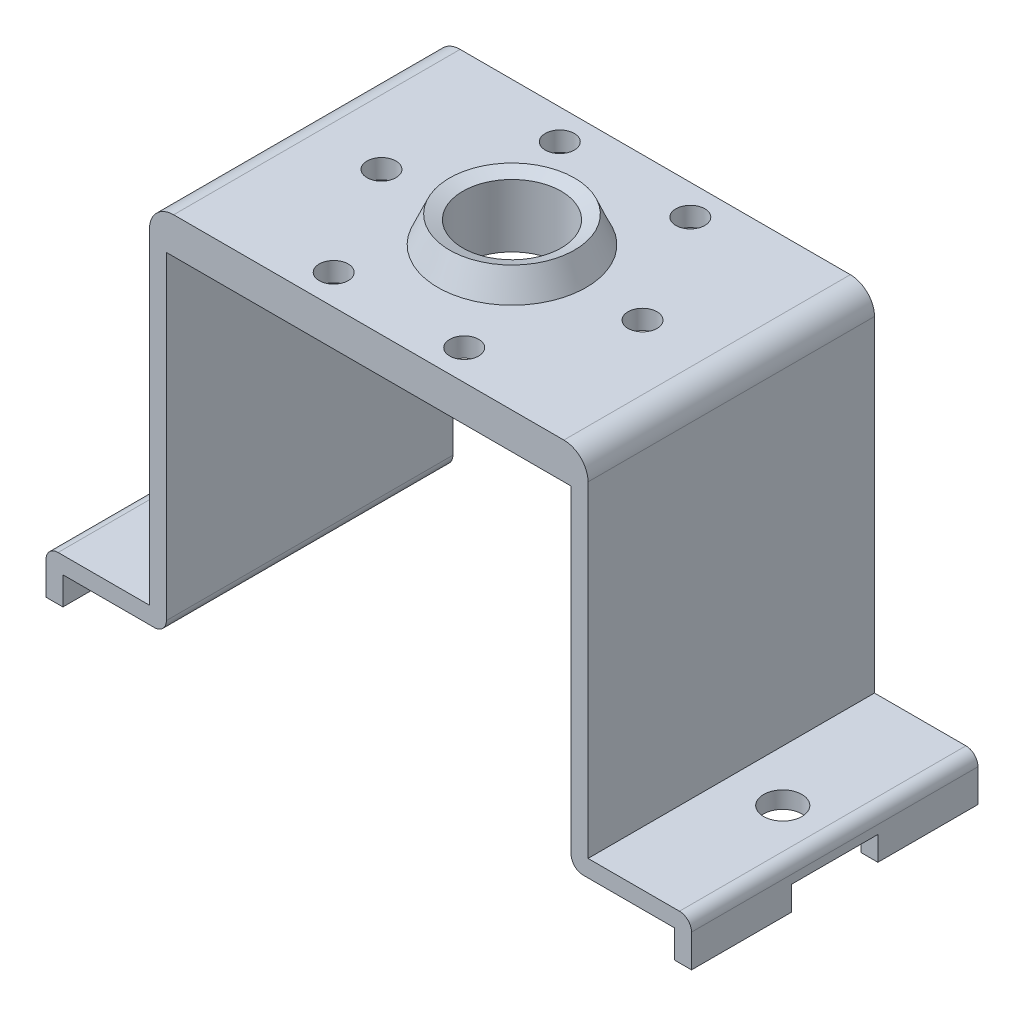
SolidWorks part; units mm, degrees
ref_plane "Front Plane" through (0, 0, 0) normal (0, 0, 1) x (1, 0, 0)
ref_plane "Top Plane" through (0, 0, 0) normal (0, 1, 0) x (1, 0, 0)
ref_plane "Right Plane" through (0, 0, 0) normal (1, 0, 0) x (0, 0, -1)
sketch "Sketch1" plane through (0, 0, 0) normal (0, 1, 0) x (1, 0, 0)
  line L1 (-17.9768, -15.0622) -> (17.9768, -15.0622)
  line L2 (-23.0568, -9.9822) -> (-23.0568, 9.9822)
  line L3 (-17.9768, 15.0622) -> (17.9768, 15.0622)
  line L4 (23.0569, -9.9822) -> (23.0569, 9.9822)
  line L5 (-23.0568, -15.0622) -> (23.0569, 15.0622) construction
  line L6 (-23.0568, 15.0622) -> (23.0569, -15.0622) construction
  arc A0 (-17.9768, -15.0622) -> (-23.0568, -9.9822) centre (-17.9768, -9.9822) cw
  arc A1 (17.9768, -15.0622) -> (23.0569, -9.9822) centre (17.9769, -9.9822) ccw
  arc A2 (17.9768, 15.0622) -> (23.0569, 9.9822) centre (17.9769, 9.9822) cw
  arc A3 (-23.0568, 9.9822) -> (-17.9768, 15.0622) centre (-17.9768, 9.9822) cw
  circle A4 centre (0, 0) radius 7.7978
  circle A5 centre (0, 0) radius 6.5722
  circle A6 centre (0, 0) radius 5.1752
  point P0 (0, 0)
  dimension "D3" = 5.08
  dimension "D4" = 15.5956
  dimension "D5" = 13.1445
  dimension "D6" = 10.3505
  dimension "D1" = 46.1137
  dimension "D2" = 30.1244
extrude "Boss-Extrude1" add sketch "Sketch1" against normal blind 2.032 contours A3 L2 A0 L1 A1 L4 A2 L3 A4 | A4 A5 | A5 A6
sketch "Sketch2" plane through (0, 0, 0) normal (1, 0, 0) x (0, 0, -1)
  line L0 (0, 0) -> (0, 6.6036) construction
  line L1 (0, 2.794) -> (-9.9655, 2.794) construction
  line L2 (-5.1752, 2.286) -> (-6.5722, 2.794)
  line L3 (-5.1752, 0) -> (-7.7978, 0)
  line L4 (0, 0) -> (-6.5722, 0) construction
  line L5 (-5.1752, 2.286) -> (-5.1752, 0)
  line L6 (-7.7978, 0) -> (-6.5722, 2.794)
  line L8 (0, 2.286) -> (-5.1752, 2.286) construction
  dimension "D1" = 2.794
  dimension "D2" = 7.7978
  dimension "D3" = 6.5722
  dimension "D4" = 5.1752
  dimension "D5" = 2.286
  dimension "D6" = 5.1752
revolve "Revolve1" add sketch "Sketch2" angle 360 about L0
sketch "Sketch3" plane through (0, 0, 0) normal (0, 0, 1) x (1, 0, 0)
  line L0 (0, 0) -> (0, -10.5163) construction
  line L1 (23.0569, 0) -> (23.0569, -25.6535) construction
  line L3 (0, 0) -> (23.0569, 0) construction
  line L4 (23.0569, -1.27) -> (23.0569, -36.83)
  line L5 (21.7868, 0) -> (21.2789, 0)
  line L6 (21.2789, 0) -> (21.2789, -37.338)
  line L7 (22.5489, -38.608) -> (23.0569, -38.608)
  line L8 (21.2789, -38.608) -> (32.1628, -38.608) construction
  line L9 (23.0569, -38.608) -> (32.1628, -38.608)
  line L10 (-32.1627, -41.5417) -> (-33.9408, -41.5417)
  line L11 (32.1628, -36.83) -> (23.0569, -36.83)
  line L12 (32.1628, -38.608) -> (32.1628, -41.5417)
  line L13 (32.1628, -41.5417) -> (33.9408, -41.5417)
  line L14 (33.9408, -41.5417) -> (33.9408, -38.1)
  line L15 (32.6708, -36.83) -> (32.1628, -36.83)
  line L16 (32.1628, -38.608) -> (32.1628, -41.5417)
  line L17 (32.1628, -38.608) -> (32.1628, -41.5417)
  line L18 (-32.1627, -38.608) -> (-32.1627, -41.5417)
  line L19 (-33.9408, -41.5417) -> (-33.9408, -38.1)
  line L20 (-32.6707, -36.83) -> (-32.1627, -36.83)
  line L21 (-22.5489, -38.608) -> (-23.0569, -38.608)
  line L22 (-23.0569, -38.608) -> (-32.1627, -38.608)
  line L23 (-32.1627, -36.83) -> (-23.0569, -36.83)
  line L24 (-23.0569, -1.27) -> (-23.0569, -36.83)
  line L25 (-21.7868, 0) -> (-21.2789, 0)
  line L26 (-21.2789, 0) -> (-21.2789, -37.338)
  arc A0 (33.9408, -38.1) -> (32.6708, -36.83) centre (32.6708, -38.1) ccw
  arc A1 (23.0569, -1.27) -> (21.7868, 0) centre (21.7869, -1.27) ccw
  arc A2 (21.2789, -37.338) -> (22.5489, -38.608) centre (22.5489, -37.338) ccw
  arc A3 (-33.9408, -38.1) -> (-32.6707, -36.83) centre (-32.6707, -38.1) cw
  arc A4 (-21.2789, -37.338) -> (-22.5489, -38.608) centre (-22.5489, -37.338) cw
  arc A5 (-23.0569, -1.27) -> (-21.7868, 0) centre (-21.7869, -1.27) cw
  point P17 (33.9408, -36.83)
  dimension "D8" = 1.27
  dimension "D1" = 38.608
  dimension "D2" = 1.778
  dimension "D3" = 10.8839
  dimension "D4" = 1.778
  dimension "D5" = 1.778
  dimension "D6" = 1.778
  dimension "D7" = 4.7117
extrude "Boss-Extrude2" add sketch "Sketch3" along normal up to surface and the other way up to surface contours A5 L24 L23 L20 A3 L19 L10 L18 L22 L21 A4 L26 L25 | L6 A2 L7 L9 L12 L13 L14 A0 L15 L11 L4 A1 L5 up to face at (0, -1.016, 15.0622) other way up to face at (0, -1.016, -15.0622)
sketch "Sketch4" plane through (0, 0, 15.0622) normal (0, 0, 1) x (1, 0, 0)
  line L0 (21.2789, 0) -> (-21.2789, 0)
  line L1 (-17.9768, 0) -> (17.9768, 0) construction
  line L2 (-21.2789, 0) -> (-23.0569, 0)
  line L3 (-23.0569, 0) -> (-23.0569, -2.032)
  line L4 (-23.0569, -1.27) -> (-23.0569, -36.83) construction
  line L5 (-23.0569, -2.032) -> (-21.2789, -2.032)
  line L6 (-21.2789, 0) -> (-21.2789, -37.338) construction
  line L7 (-21.2789, -2.032) -> (-17.9768, -2.032)
  line L8 (-17.9768, -2.032) -> (-17.9768, 0)
  line L9 (0, 0) -> (0, -5.6499) construction
  line L10 (17.9768, -2.032) -> (17.9768, 0)
  line L11 (21.2789, -2.032) -> (17.9768, -2.032)
  line L12 (23.0569, -2.032) -> (21.2789, -2.032)
  line L13 (21.2789, 0) -> (23.0569, 0)
  line L14 (23.0569, 0) -> (23.0569, -2.032)
  arc M8 (-21.7868, 0) -> (-23.0569, -1.27) centre (-21.7869, -1.27) ccw
  line M9 (-23.0569, -1.27) -> (-23.0569, -36.83)
  line M17 (-21.2789, -37.338) -> (-21.2789, 0)
  line M18 (-21.2789, 0) -> (-21.7868, 0)
  dimension "D1" = 1.778
extrude "Boss-Extrude3" add sketch "Sketch4" against normal up to surface (30.1244 mm away) contours L2 L3 M8 | L5 M9 M17 M18 M8 | L7 L8 L0 M17 | L14 L13 L0 L10 L11 L12 up to face at (0, -1.016, -15.0622)
fillet "Fillet1" radius 2.54 1 edges at (23.0569, 0, 0)
fillet "Fillet2" radius 2.54 1 edges at (-23.0569, 0, 0)
sketch "Sketch5" plane through (-33.9408, 0, 0) normal (-1, 0, 0) x (0, 0, 1)
  line L0 (0, 0) -> (0, -41.5417) construction
  line L1 (15.0622, -41.5417) -> (-15.0622, -41.5417) construction
  line L3 (-4.5339, -39.0017) -> (4.5339, -39.0017)
  line L4 (-4.5339, -39.0017) -> (-4.5339, -41.5417)
  line L5 (4.5339, -39.0017) -> (4.5339, -41.5417)
  line L6 (-4.5339, -41.5417) -> (4.5339, -41.5417)
  point P9 (0, -39.0017)
  dimension "D1" = 9.0678
  dimension "D2" = 2.54
  dimension "D3" = 4.5339
extrude "Cut-Extrude1" cut sketch "Sketch5" against normal blind 116.84
sketch "Sketch6" plane through (0, -36.83, 0) normal (0, 1, 0) x (1, 0, 0)
  line L0 (-32.6707, -15.0622) -> (-32.6707, 15.0622) construction
  line L1 (0, 0) -> (0, -33.0062) construction
  circle A0 centre (-28.4734, 0) radius 2.0129
  circle A1 centre (28.4734, 0) radius 2.0129
  point P4 (-32.6708, 0)
  dimension "D1" = 4.1974
  dimension "D2" = 4.0259
  dimension "D3" = 28.4734
extrude "Cut-Extrude2" cut sketch "Sketch6" against normal through all
sketch "Sketch7" plane through (0, 0, 0) normal (0, 1, 0) x (1, 0, 0)
  line L0 (0, 0) -> (0, -17.2763) construction
  line L1 (0, 0) -> (13.7258, 0) construction
  line L2 (0, 0) -> (-6.8629, -11.8869) construction
  circle A0 centre (13.7258, 0) radius 1.524
  circle A1 centre (-13.7258, 0) radius 1.524
  circle A2 centre (-6.8629, -11.8869) radius 1.524
  circle A3 centre (6.8629, 11.8869) radius 1.524
  circle A4 centre (-6.8629, 11.8869) radius 1.524
  circle A5 centre (6.8629, -11.8869) radius 1.524
  dimension "D2" = 3.048
  dimension "D1" = 13.7258
  dimension "D4" = 120
  dimension "D5" = 13.7258
  dimension "D6" = 13.7258
  dimension "D3" = 3
extrude "Cut-Extrude3" cut sketch "Sketch7" against normal through all
sketch "Sketch8" plane through (-23.0568, 0, 0) normal (-1, 0, 0) x (0, 0, 1)
  line L0 (0, -29.543) -> (0, 0) construction
  line L1 (0, -11.6475) -> (9.0678, -11.6475) construction
  line L2 (0, -11.6475) -> (-9.0678, -11.6475) construction
  line L3 (-9.0678, -11.6475) -> (-9.0678, -41.5417) construction
  line L4 (9.0678, -11.6475) -> (9.0678, -41.5417) construction
  line L5 (-4.5339, -41.5417) -> (-15.0622, -41.5417) construction
  line L6 (15.0622, -41.5417) -> (4.5339, -41.5417) construction
  line L7 (-15.0622, -2.54) -> (-9.0678, -41.5417)
  line L8 (9.0678, -41.5417) -> (15.0622, -2.54)
  line L9 (-15.0622, -2.54) -> (-15.0622, -41.5417)
  line L10 (-15.0622, -41.5417) -> (-9.0678, -41.5417)
  line L11 (9.0678, -41.5417) -> (15.0622, -41.5417)
  line L12 (15.0622, -41.5417) -> (15.0622, -2.54)
  point P11 (-9.798, -41.5417)
  point P12 (0, 0)
  point P15 (9.7981, -41.5417)
  dimension "D1" = 18.1356
  dimension "D2" = 11.6475
ref_plane "Plane1" through (0, -1.016, 0) normal (0, 1, 0) x (1, 0, 0)
mirror "Mirror4" about plane through (0, -1.016, 0) normal (0, 1, 0) of "Revolve1"
sketch "Sketch9" plane through (0, -2.032, 0) normal (0, -1, 0) x (1, 0, 0)
  line L0 (-21.2789, 15.0622) -> (21.2789, 15.0622)
  line L1 (21.2789, 15.0622) -> (21.2789, -15.0622)
  line L2 (21.2789, -15.0622) -> (-21.2789, -15.0622)
  line L3 (-21.2789, -15.0622) -> (21.2789, -15.0622) construction
  line L4 (-21.2789, 15.0622) -> (-21.2789, -15.0622) construction
  line L5 (-21.2789, -15.0622) -> (-21.2789, 15.0622)
  line L6 (-19.5009, 13.2842) -> (19.5009, 13.2842)
  line L7 (19.5009, 13.2842) -> (19.5009, -13.2842)
  line L8 (19.5009, -13.2842) -> (-19.5009, -13.2842)
  line L9 (-19.5009, -13.2842) -> (-19.5009, 13.2842)
  dimension "D1" = 1.778
extrude "Boss-Extrude4" add sketch "Sketch9" along normal blind 1.778
